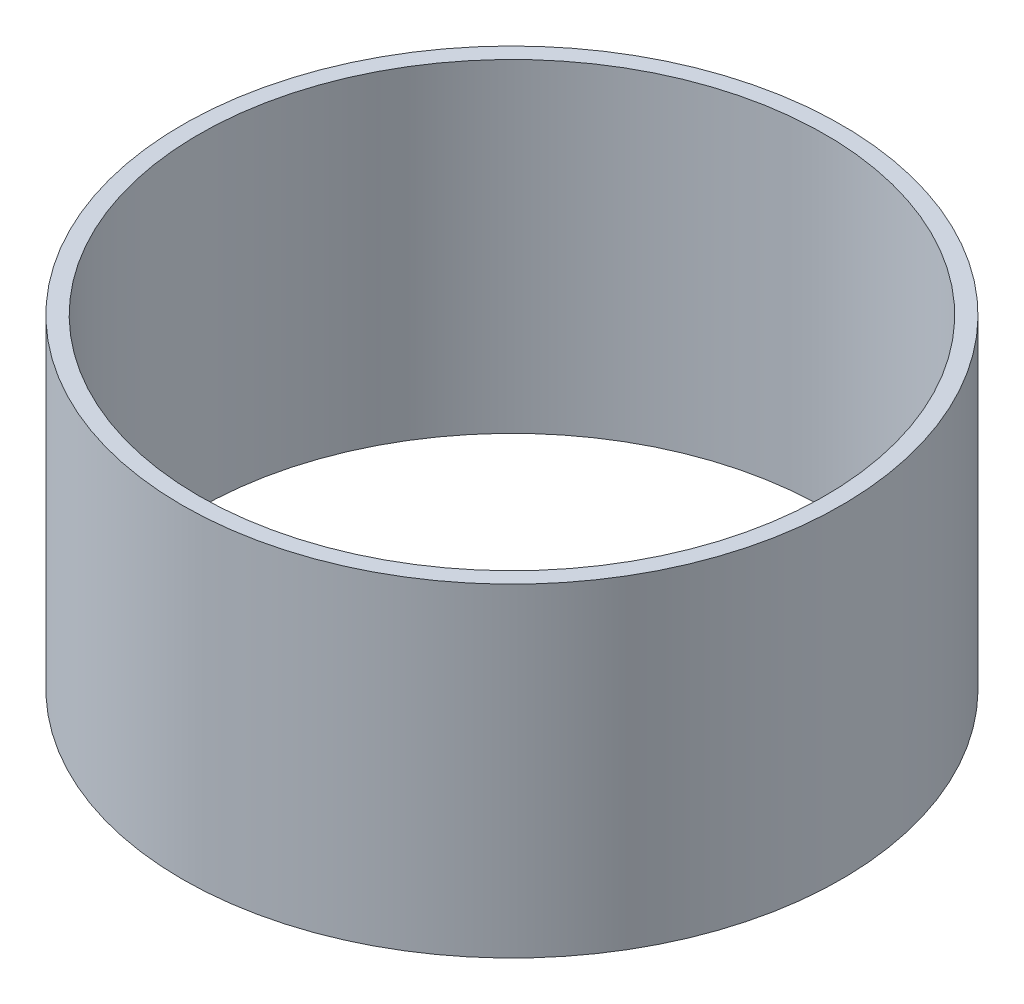
SolidWorks part; units mm, degrees
material "1060 合金"
ref_plane "前视基准面" through (0, 0, 0) normal (0, 0, 1) x (1, 0, 0)
ref_plane "上视基准面" through (0, 0, 0) normal (0, 1, 0) x (1, 0, 0)
ref_plane "右视基准面" through (0, 0, 0) normal (1, 0, 0) x (0, 0, -1)
other "Configuration Table"
sketch "草图1" plane through (0, 0, 0) normal (0, 1, 0) x (1, 0, 0)
  circle A0 centre (0, 0) radius 40
  circle A1 centre (0, 0) radius 38
extrude "凸台-拉伸1" add sketch "草图1" along normal blind 39.3
